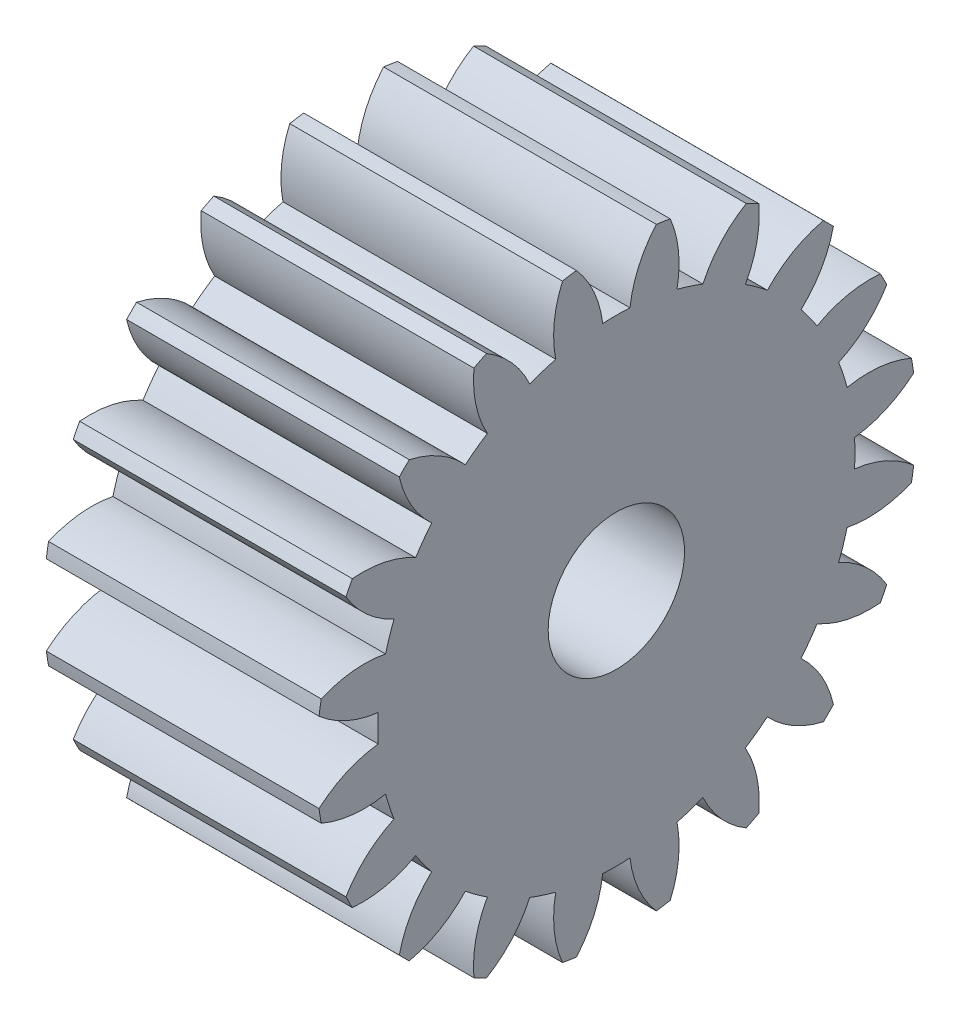
SolidWorks part; units mm, degrees
ref_plane "Plane1" through (0, 0, 0) normal (0, 0, 1) x (1, 0, 0)
ref_plane "Plane2" through (0, 0, 0) normal (0, 1, 0) x (1, 0, 0)
ref_plane "Plane3" through (0, 0, 0) normal (1, 0, 0) x (0, 0, -1)
other "Configuration Table"
sketch "HoldingSke" plane through (0, 0, 0) normal (0, 1, 0) x (1, 0, 0)
  line L0 (0, 0) -> (0.9397, -0.342)
  line L1 (-15, 0) -> (100, 0) construction
  line L2 (0, 0) -> (-2.1039, 2.3779)
  line L3 (0, 0) -> (-11.863, 4.5341)
  line L4 (0, 0) -> (8.1152, 2.9537)
  line L5 (0, 0) -> (-46.8476, -17.4728)
  line L6 (0, 0) -> (-8.2896, -5.593)
  line L7 (-2.1039, 2.3779) -> (8.6586, 51.2059)
  line L8 (-76.2, 54.61) -> (-75.3, 54.61)
  line L9 (-71.009, 38.7566) -> (-53.1078, 45.2721)
  line L10 (-76.2, 71.12) -> (104.1128, 71.12)
  line L11 (0, 0) -> (-10, 0)
  line L12 (-76.2, 101.6) -> (-76.162, 101.6)
  line L13 (24.9733, 27.94) -> (52.9518, 28.4284)
  line L14 (24.9733, 27.94) -> (24.9743, 27.94)
  line L15 (24.9733, 27.94) -> (100.4006, 29.5858)
  line L16 (-63.627, -1) -> (-12.827, -1)
  circle A0 centre (0, 0) radius 2.5
  circle A1 centre (0, 0) radius 8.749
  circle A2 centre (0, 0) radius 37.5
  circle A3 centre (0, 0) radius 2.5
  dimension "MHD" = 17.498
  dimension "Hub_dia" = 75
  dimension "Bore" = 5
  dimension "MBD" = 5
  dimension "Num_teeth" = 20
  dimension "Pitch" = 1
  dimension "Overall_len" = 50
  dimension "Show_teeth" = 20
  dimension "Thickness" = 10
  dimension "OAL" = 50.0001
  dimension "T_dim" = 0.9
  dimension "Ap" = 20
  dimension "H" = 19.05
  dimension "Pitch_radius" = 180.3128
  dimension "Width" = 10
  dimension "Backlash" = 0.038
  dimension "Addendum_fac" = 1
  dimension "Dedendum_fac" = 1.25
  dimension "Clearance_fac" = 0.25
  dimension "Dedendum_add" = 0.001
  dimension "Module" = 1
sketch "BasProSke" plane through (0, 0, 0) normal (0, 1, 0) x (1, 0, 0)
  line L0 (-10, 0) -> (60, 0) construction
  line L1 (0, 0) -> (0, 11)
  line L2 (0, 0) -> (10, 0)
  line L3 (10, 0) -> (10, 11)
  line L4 (10, 11) -> (0, 11)
  dimension "Thickness" = 10
  dimension "Diameter" = 22
revolve "Base-Revolve" add sketch "BasProSke" angle 360 about L0
sketch "TooCutSke" plane through (0, 0, 0) normal (1, 0, 0) x (0, 0, -1)
  line L1 (0, 0) -> (0, 107) construction
  line L2 (0, 0) -> (-0.8511, 9.9637) construction
  line L3 (0, 0) -> (-3.1206, 19.7028) construction
  line L4 (-0.8511, 9.9637) -> (-1.5603, 9.8514) construction
  arc A0 (0.4999, 8.7347) -> (-0.4999, 8.7347) centre (0, 0) ccw
  arc A1 (1.4852, 10.9249) -> (-1.4852, 10.9249) centre (0, 0) ccw
  circle A2 centre (0, 0) radius 10 construction
  circle A3 centre (0, 0) radius 9.3969 construction
  arc A4 (-0.4999, 8.7347) -> (-1.4852, 10.9249) centre (-4.4722, 8.2645) ccw
  arc A5 (1.4852, 10.9249) -> (0.4999, 8.7347) centre (4.4722, 8.2645) ccw
  dimension "Root_dia" = 17.498
  dimension "Overcut_dia" = 22.0508
  dimension "Pitch_dia" = 20
  dimension "Base_dia" = 18.7939
  dimension "Flank_rad" = 4
  dimension "Half_ang" = 9
  dimension "Half_CT" = 0.7181
extrude "ToothCut" cut sketch "TooCutSke" along normal through all
fillet "Breaks" [suppressed] radius 0.02
fillet "RootFillets" [suppressed] radius 0.251
pattern_circular "TeethCuts" count 20 every 18 about axis through (-10, 0, 0) along (1, 0, 0) of "ToothCut", "RootFillets", "Breaks"
sketch "HubNeaOneSke" plane through (0, 0, 0) normal (-1, 0, 0) x (0, 0, 1)
  circle A0 centre (0, 0) radius 8.749
  dimension "Diameter" = 17.498
extrude "HubNearOne" [suppressed] add sketch "HubNeaOneSke" along normal blind 40.0001
sketch "HubNeaBotSke" plane through (0, 0, 0) normal (-1, 0, 0) x (0, 0, 1)
  circle A0 centre (0, 0) radius 8.749
  dimension "Diameter" = 17.498
extrude "HubNearBoth" [suppressed] add sketch "HubNeaBotSke" along normal blind 20
ref_plane "FarPln" through (10, 0, 0) normal (1, 0, 0) x (0, 0, -1)
sketch "HubFarSke" plane through (10, 0, 0) normal (1, 0, 0) x (0, 0, -1)
  circle A0 centre (0, 0) radius 8.749
  dimension "Diameter" = 17.498
extrude "HubFar" [suppressed] add sketch "HubFarSke" along normal blind 20
sketch "BorSke" plane through (0, 0, 0) normal (1, 0, 0) x (0, 0, -1)
  circle A0 centre (0, 0) radius 2.5
  dimension "Diameter" = 5
extrude "Bore" cut sketch "BorSke" along normal mid plane 100.0001
sketch "KeySke" plane through (0, 0, 0) normal (1, 0, 0) x (0, 0, -1)
  line L0 (-1, 0) -> (-1, 3.4)
  line L1 (-1, 3.4) -> (1, 3.4)
  line L2 (1, 3.4) -> (1, 0)
  line L3 (0, 0) -> (0, 34) construction
  line L4 (-1, 0) -> (1, 0)
  dimension "Offset" = 3.4
  dimension "Width" = 2
extrude "Keyway" [suppressed] cut sketch "KeySke" along normal mid plane 100.0001
pattern_circular "Keyway2" [suppressed] count 2 every 90 about axis through (-10, 0, 0) along (1, 0, 0)
equation "' \"Module@HoldingSke\" = 6.35"
equation "' \"Num_teeth@HoldingSke\" = 12"
equation "' \"Ap@HoldingSke\" =  20"
equation "' \"Ap@HoldingSke\" = 20"
equation "' \"Width@HoldingSke\" = 0.5 * 25.4"
equation "' \"Hub_dia@HoldingSke\"= 1 * 25.4"
equation "' \"Hub_dia@HoldingSke\" = 1 * 25.4"
equation "' \"Overall_len@HoldingSke\" = 1.0 * 25.4"
equation "' \"Bore@HoldingSke\" = 0.75 * 25.4"
equation "' \"T_dim@HoldingSke\" = 0.1 * 25.4"
equation "' \"Width@KeySke\" = 0.25 * 25.4"
equation "' \"Show_teeth@HoldingSke\" = 13"
equation "' \"Backlash@HoldingSke\" = 0.009 * 25.4"
equation "' \"Addendum_fac@HoldingSke\" = 1.0"
equation "' \"Dedendum_fac@HoldingSke\" = 1.25"
equation "' \"Dedendum_add@HoldingSke\" = 0.00005 * 25.4"
equation "' \"Clearance_fac@HoldingSke\" = 0.25"
equation "\"Pitch@HoldingSke\" = 1 / \"Module@HoldingSke\""
equation "\"Overcut_dia@TooCutSke\" = (\"Num_teeth@HoldingSke\" + 2 * \"Addendum_fac@HoldingSke\") / \"Pitch@HoldingSke\" + 0.002 * 25.4"
equation "\"Pitch_dia@TooCutSke\" = \"Num_teeth@HoldingSke\" / \"Pitch@HoldingSke\""
equation "\"Base_dia@TooCutSke\" = \"Num_teeth@HoldingSke\" / \"Pitch@HoldingSke\" * cos((\"Ap@HoldingSke\"  * 3.14159265 / 180))"
equation "\"Root_dia@TooCutSke\" = (\"Num_teeth@HoldingSke\" + 2) / \"Pitch@HoldingSke\" - 2 * (\"Addendum_fac@HoldingSke\" + \"Dedendum_fac@HoldingSke\") / \"Pitch@HoldingSke\" - \"Dedendum_add@HoldingSke\" * 2"
equation "\"Half_ang@TooCutSke\" = 180 / \"Num_teeth@HoldingSke\""
equation "\"Half_CT@TooCutSke\" = \"Num_teeth@HoldingSke\" / \"Pitch@HoldingSke\" * sin((3.14159265 / 2 / \"Num_teeth@HoldingSke\")) / 2 - 7 * \"Backlash@HoldingSke\" / 4"
equation "\"Flank_rad@TooCutSke\" = \"Num_teeth@HoldingSke\" / \"Pitch@HoldingSke\" / 5"
equation "\"Radius@RootFillets\" = \"Clearance_fac@HoldingSke\" / \"Pitch@HoldingSke\" + \"Dedendum_add@HoldingSke\""
equation "\"Break_rad@Breaks\" = 0.02 / \"Pitch@HoldingSke\""
equation "\"Thickness@HoldingSke\" = \"Width@HoldingSke\""
equation "\"OAL@HoldingSke\" = \"Thickness@HoldingSke\""
equation "\"MHD@HoldingSke\" = (\"Num_teeth@HoldingSke\" + 2) / \"Pitch@HoldingSke\" - 2 * (\"Addendum_fac@HoldingSke\" + \"Dedendum_fac@HoldingSke\")  / \"Pitch@HoldingSke\" - \"Dedendum_add@HoldingSke\" * 2"
equation "\"MBD@HoldingSke\" = (\"Num_teeth@HoldingSke\" + 2) / \"Pitch@HoldingSke\" - 2 * (\"Addendum_fac@HoldingSke\" + \"Dedendum_fac@HoldingSke\")  / \"Pitch@HoldingSke\" - \"Dedendum_add@HoldingSke\" * 2 - 0.002 * 25.4"
equation "\"MHD@HoldingSke\" = ((sgn( \"MHD@HoldingSke\" - \"Hub_dia@HoldingSke\" )-1)*( \"MHD@HoldingSke\" - \"Hub_dia@HoldingSke\" ))/-2+ \"Hub_dia@HoldingSke\""
equation "\"MBD@HoldingSke\" = ((sgn( \"MBD@HoldingSke\" - \"Bore@HoldingSke\" )-1)*( \"MBD@HoldingSke\" - \"Bore@HoldingSke\" ))/-2+ \"Bore@HoldingSke\""
equation "\"OAL@HoldingSke\" = ((sgn( \"OAL@HoldingSke\" - \"Overall_len@HoldingSke\" )+1)*( \"OAL@HoldingSke\" - \"Overall_len@HoldingSke\" ))/2 + \"Overall_len@HoldingSke\" + 0.000002 * 25.4"
equation "\"Num_teeth@TeethCuts\" = int( \"Show_teeth@HoldingSke\" ) + 1"
equation "\"Num_teeth@TeethCuts\" = ((sgn( \"Num_teeth@TeethCuts\" - \"Num_teeth@HoldingSke\" )-1)*( \"Num_teeth@TeethCuts\" - \"Num_teeth@HoldingSke\" ))/-2+ \"Num_teeth@HoldingSke\""
equation "\"Num_teeth@TeethCuts\" = ((sgn( \"Num_teeth@TeethCuts\" - 2.0)+1)*( \"Num_teeth@TeethCuts\" - 2.0))/2 +2.0"
equation "\"Angle@TeethCuts\" = 360.0 / \"Num_teeth@HoldingSke\""
equation "\"Diameter@BasProSke\" = (\"Num_teeth@HoldingSke\" + 2 * \"Addendum_fac@HoldingSke\") / \"Pitch@HoldingSke\""
equation "\"Thickness@BasProSke\"  = \"Thickness@HoldingSke\""
equation "' \"Fillet_rad@BasProSke\" =  \"Thickness@HoldingSke\" * 0.05"
equation "' \"Fillet_rad@BasProSke\" = \"Thickness@HoldingSke\" * 0.05"
equation "\"MHD@HoldingSke\" = ((sgn( \"MHD@HoldingSke\" - \"Root_dia@TooCutSke\" )-1)*( \"MHD@HoldingSke\" - \"Root_dia@TooCutSke\" ))/-2+ \"Root_dia@TooCutSke\""
equation "\"Diameter@HubNeaOneSke\" = \"MHD@HoldingSke\""
equation "\"Length@HubNearOne\" = \"OAL@HoldingSke\" - \"Thickness@BasProSke\""
equation "\"Diameter@HubNeaBotSke\" = \"MHD@HoldingSke\""
equation "\"Length@HubNearBoth\" = ( \"OAL@HoldingSke\" - \"Thickness@BasProSke\" ) / 2.0"
equation "\"Thickness@FarPln\" = \"Thickness@BasProSke\""
equation "\"Diameter@HubFarSke\" = \"MHD@HoldingSke\""
equation "\"Length@HubFar\" = ( \"OAL@HoldingSke\" - \"Thickness@BasProSke\" ) / 2.0"
equation "\"Diameter@BorSke\" = \"MBD@HoldingSke\""
equation "\"D1@Bore\" = \"OAL@HoldingSke\" * 2.0"
equation "\"D1@Keyway\" = \"OAL@HoldingSke\" * 2.0"
equation "\"Offset@KeySke\" = \"T_dim@HoldingSke\" + \"MBD@HoldingSke\" / 2.0"
